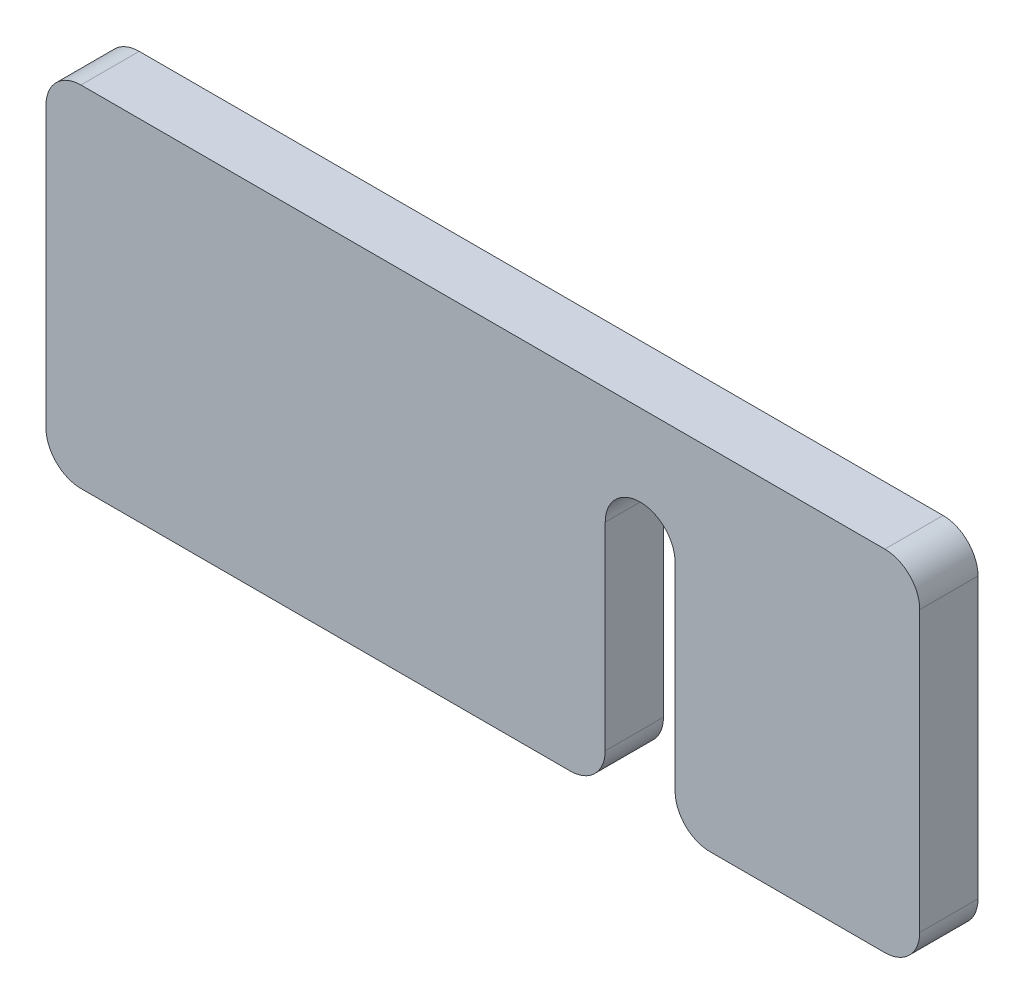
SolidWorks part; units mm, degrees
ref_plane "Plan de face" through (0, 0, 0) normal (0, 0, 1) x (1, 0, 0)
ref_plane "Plan de dessus" through (0, 0, 0) normal (0, 1, 0) x (1, 0, 0)
ref_plane "Plan de droite" through (0, 0, 0) normal (1, 0, 0) x (0, 0, -1)
sketch "Esquisse1" plane through (0, 0, 0) normal (0, 0, 1) x (1, 0, 0)
  line L0 (-37.5, 0) -> (37.5, 0)
other "Elément mécano-soudé1"
ref_plane "Plan1" through (-37.5, 0, 0) normal (1, 0, 0) x (0, 1, 0)
sketch "plat" plane through (-37.5, 0, 0) normal (1, 0, 0) x (0, 1, 0)
  line L0 (-15, 0) -> (15, 0) construction
  line L1 (-15, 2.5) -> (15, 2.5)
  line L2 (-15, 2.5) -> (-15, -2.5)
  line L3 (-15, -2.5) -> (15, -2.5)
  line L4 (15, 2.5) -> (15, -2.5)
  line L5 (0, 2.5) -> (0, -2.5) construction
  point P8 (0, 0)
  dimension "B" = 30
  dimension "A" = 5
sketch "Esquisse2" plane through (0, 0, -2.5) normal (0, 0, -1) x (-1, 0, 0)
  line L0 (-37.5, -15) -> (37.5, -15) construction
  line L1 (-16.5, -15) -> (-10.5, -15)
  line L2 (-16.5, -15) -> (-16.5, 5)
  line L4 (-10.5, -15) -> (-10.5, 5)
  line L5 (-37.5, -15) -> (-37.5, 15) construction
  arc A0 (-16.5, 5) -> (-10.5, 5) centre (-13.5, 5) cw
  dimension "D1" = 6
  dimension "D2" = 20
  dimension "D3" = 21
extrude "Enlèv. mat.-Extru.1" cut sketch "Esquisse2" against normal through all
fillet "Congé1" radius 3 6 edges at (37.5, 15, 0) (37.5, -15, 0) (16.5, -15, 0) (10.5, -15, 0) (-37.5, 15, 0) (-37.5, -15, 0)
